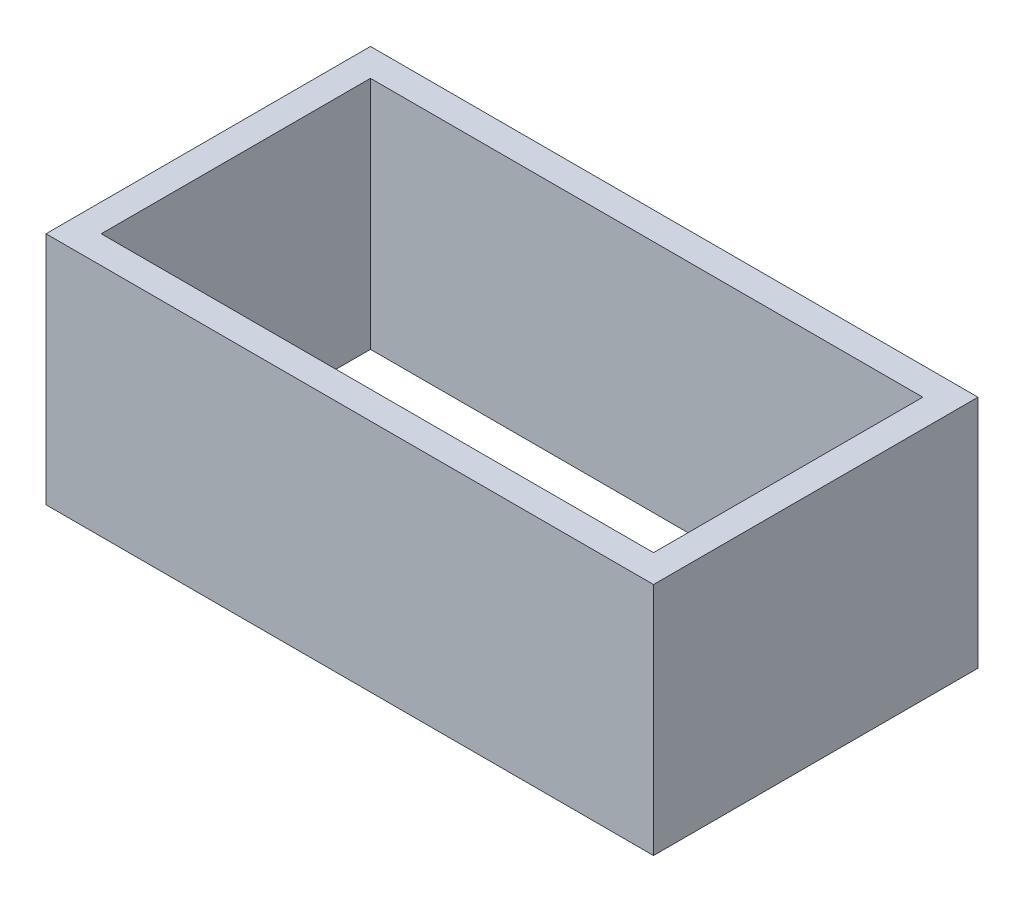
SolidWorks part; units mm, degrees
ref_plane "Front Plane" through (0, 0, 0) normal (0, 0, 1) x (1, 0, 0)
ref_plane "Top Plane" through (0, 0, 0) normal (0, 1, 0) x (1, 0, 0)
ref_plane "Right Plane" through (0, 0, 0) normal (1, 0, 0) x (0, 0, -1)
sketch "Sketch1" plane through (0, 0, 0) normal (0, 1, 0) x (1, 0, 0)
  line L0 (-22, -11.75) -> (-22, 11.75)
  line L1 (20, -9.75) -> (-20, -9.75)
  line L2 (20, -9.75) -> (20, 9.75)
  line L3 (20, 9.75) -> (-20, 9.75)
  line L4 (-20, -9.75) -> (-20, 9.75)
  line L5 (20, -9.75) -> (-20, 9.75) construction
  line L6 (20, 9.75) -> (-20, -9.75) construction
  line L7 (22, 11.75) -> (-22, 11.75)
  line L8 (22, -11.75) -> (22, 11.75)
  line L9 (22, -11.75) -> (-22, -11.75)
  point P0 (0, 0)
  dimension "D1" = 40
  dimension "D2" = 19.5
  dimension "D3" = 2
extrude "Boss-Extrude1" add sketch "Sketch1" along normal blind 17
